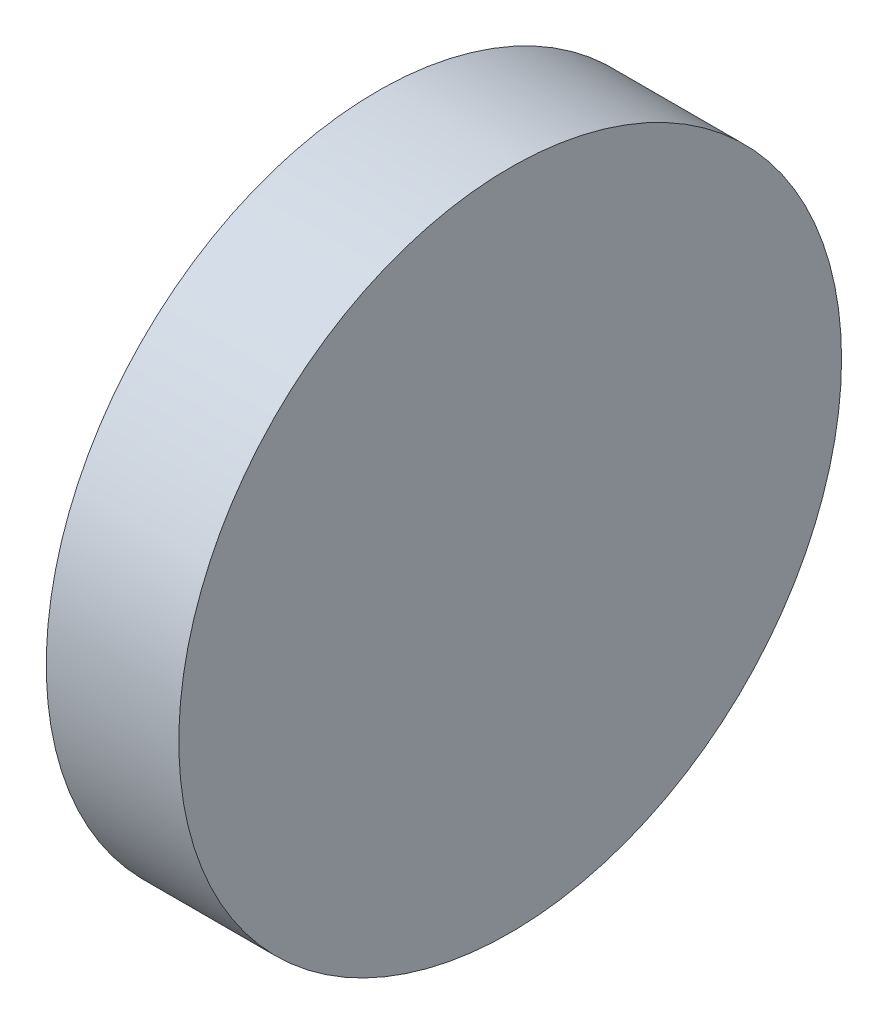
SolidWorks part; units mm, degrees
ref_plane "前视基准面" through (0, 0, 0) normal (0, 0, 1) x (1, 0, 0)
ref_plane "上视基准面" through (0, 0, 0) normal (0, 1, 0) x (1, 0, 0)
ref_plane "右视基准面" through (0, 0, 0) normal (1, 0, 0) x (0, 0, -1)
sketch "草图1" plane through (0, 0, 0) normal (0, 0, 1) x (1, 0, 0)
  line L0 (500.7376, 154.5864) -> (553.591, 155.1295) construction
  line L1 (530.576, 154.893) -> (520.576, 154.893)
  line L3 (530.576, 154.893) -> (530.576, 129.893)
  line L4 (530.576, 129.893) -> (520.576, 129.893)
  line L5 (520.576, 129.893) -> (520.576, 154.893)
  dimension "D1" = 25
  dimension "D2" = 10
revolve "旋转1" add sketch "草图1" angle 360 about L1
